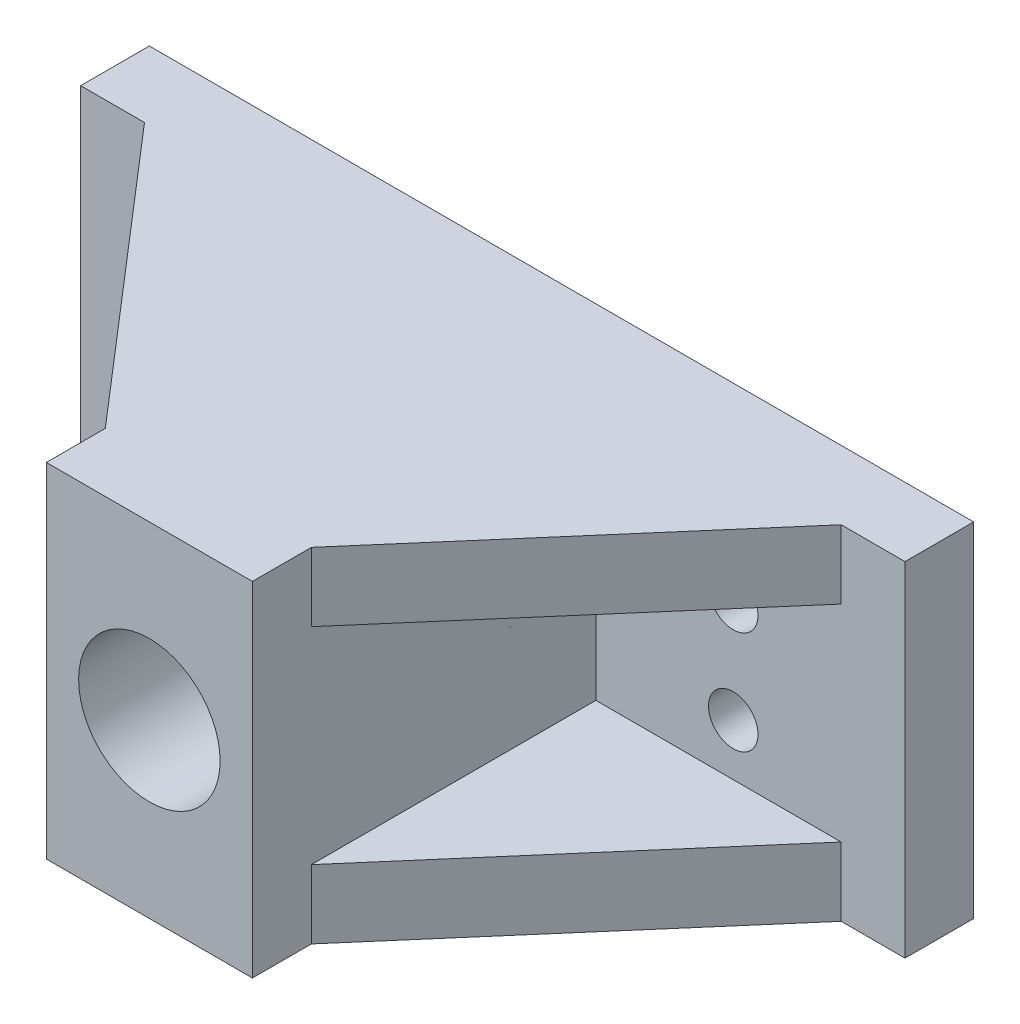
SolidWorks part; units mm, degrees
ref_plane "前视基准面" through (0, 0, 0) normal (0, 0, 1) x (1, 0, 0)
ref_plane "上视基准面" through (0, 0, 0) normal (0, 1, 0) x (1, 0, 0)
ref_plane "右视基准面" through (0, 0, 0) normal (1, 0, 0) x (0, 0, -1)
sketch "草图1" plane through (0, 0, 0) normal (0, 0, 1) x (1, 0, 0)
  line L1 (20, -7.5) -> (-20, -7.5)
  line L2 (20, -7.5) -> (20, 7.5)
  line L3 (20, 7.5) -> (-20, 7.5)
  line L4 (-20, -7.5) -> (-20, 7.5)
  line L5 (0, 7.5) -> (0, -7.5) construction
  line L6 (20, 0) -> (-20, 0) construction
  point P0 (0, 0)
  dimension "D1" = 15
  dimension "D2" = 40
extrude "凸台-拉伸1" add sketch "草图1" along normal blind 5
sketch "草图2" plane through (0, 0, 5) normal (0, 0, 1) x (1, 0, 0)
  line L0 (0, 0) -> (0, 16.7809) construction
  circle A0 centre (0, 0) radius 5.15
  circle A1 centre (-12, 0) radius 1.8
  circle A2 centre (12, 0) radius 1.8
  dimension "D1" = 10.3
  dimension "D2" = 3.6
  dimension "D3" = 12
extrude "切除-拉伸1" cut sketch "草图2" against normal blind 5
sketch "草图3" plane through (0, 0, 5) normal (0, 0, 1) x (1, 0, 0)
  line L0 (-7.5, 7.5) -> (-7.5, -7.5)
  line L1 (20, 7.5) -> (-20, 7.5) construction
  line L2 (-20, -7.5) -> (20, -7.5) construction
  line L3 (0, 7.5) -> (0, -7.5) construction
  line L4 (7.5, 7.5) -> (7.5, -7.5)
  line L5 (-7.5, 7.5) -> (7.5, 7.5)
  line L6 (-7.5, -7.5) -> (7.5, -7.5)
  circle A0 centre (0, 0) radius 5.05
  dimension "D1" = 15
extrude "凸台-拉伸2" add sketch "草图3" along normal blind 25
sketch "草图4" plane through (0, 0, 5) normal (0, 0, -1) x (-1, 0, 0)
  circle A0 centre (0, 0) radius 5.5
extrude "切除-拉伸2" cut sketch "草图4" against normal blind 31
sketch "草图5" plane through (0, 0, 5) normal (0, 0, 1) x (1, 0, 0)
  line L0 (-20, 7.5) -> (-30, 7.5)
  line L1 (-30, 7.5) -> (-30, -7.5)
  line L2 (-30, -7.5) -> (-20, -7.5)
  line L3 (-20, -7.5) -> (-20, 7.5)
  line L4 (0, 7.5) -> (0, -7.5) construction
  line L5 (7.5, 7.5) -> (-7.5, 7.5) construction
  line L6 (-7.5, -7.5) -> (7.5, -7.5) construction
  line L7 (30, -7.5) -> (20, -7.5)
  line L8 (20, -7.5) -> (20, 7.5)
  line L9 (20, 7.5) -> (30, 7.5)
  line L10 (30, 7.5) -> (30, -7.5)
  dimension "D1" = 10
extrude "凸台-拉伸3" add sketch "草图5" against normal blind 5
sketch "草图6" plane through (0, 0, 5) normal (0, 0, 1) x (1, 0, 0)
  line L0 (0, 0) -> (0, 14.0477) construction
  circle A0 centre (-24, 0) radius 1.8
  circle A1 centre (24, 0) radius 1.8
  circle A2 centre (-12, 0) radius 1.8 construction
  dimension "D1" = 3.6
  dimension "D2" = 12
extrude "切除-拉伸3" cut sketch "草图6" against normal blind 5
sketch "草图7" plane through (0, 0, 5) normal (0, 0, 1) x (1, 0, 0)
  line L0 (-30, 7.5) -> (-30, 12.5)
  line L1 (-30, 12.5) -> (30, 12.5)
  line L2 (30, 12.5) -> (30, 7.5)
  line L3 (30, 7.5) -> (-30, 7.5)
  line L4 (0, 0) -> (-30, 0) construction
  line L5 (-30, 7.5) -> (-30, -7.5) construction
  line L6 (-30, -12.5) -> (30, -12.5)
  line L7 (30, -12.5) -> (30, -7.5)
  line L8 (30, -7.5) -> (-30, -7.5)
  line L9 (-30, -7.5) -> (-30, -12.5)
  dimension "D1" = 5
extrude "凸台-拉伸4" add sketch "草图7" against normal blind 5
sketch "草图8" plane through (0, 0, 5) normal (0, 0, 1) x (1, 0, 0)
  line L0 (-7.5, 7.5) -> (-7.5, 12.5)
  line L1 (30, 12.5) -> (-30, 12.5) construction
  line L2 (-7.5, 12.5) -> (7.5, 12.5)
  line L3 (7.5, 12.5) -> (7.5, 7.5)
  line L4 (7.5, 7.5) -> (-7.5, 7.5)
  line L5 (-7.5, -7.5) -> (-7.5, -12.5)
  line L6 (-30, -12.5) -> (30, -12.5) construction
  line L7 (-7.5, -12.5) -> (7.5, -12.5)
  line L8 (7.5, -12.5) -> (7.5, -7.5)
  line L9 (7.5, -7.5) -> (-7.5, -7.5)
extrude "凸台-拉伸5" add sketch "草图8" along normal up to surface (25 mm away) up to face at (-5.5, 0, 30)
sketch "草图9" plane through (0, 12.5, 0) normal (0, 1, 0) x (1, 0, 0)
  line L0 (-25.3552, -5) -> (-7.5, -25.7076)
  line L1 (-7.5, -5) -> (-30, -5) construction
  line L2 (-7.5, -30) -> (-7.5, -5) construction
rib "筋1" sketch "草图9" sketch "草图9" thickness 5 extrusion direction parallel to sketch draft on no parameters "D1"=5
ref_plane "基准面1" through (0, 0, 0) normal (0, 1, 0) x (1, 0, 0)
mirror "镜向1" about plane through (0, 0, 0) normal (0, 1, 0) of "筋1"
ref_plane "基准面3" through (0, 0, 0) normal (-1, 0, 0) x (0, 0, 1)
mirror "镜向2" about plane through (0, 0, 0) normal (-1, 0, 0) of "镜向1", "筋1"
sketch "草图11" plane through (0, 0, 5) normal (0, 0, 1) x (1, 0, 0)
  circle A0 centre (-24, 0) radius 1.8
  circle A1 centre (-12, 0) radius 1.8
  circle A2 centre (12, 0) radius 1.8
  circle A3 centre (24, 0) radius 1.8
extrude "凸台-拉伸6" add sketch "草图11" against normal blind 5
sketch "草图12" plane through (0, 0, 5) normal (0, 0, 1) x (1, 0, 0)
  line L0 (0, 0) -> (-41.3935, 0) construction
  line L1 (-7.5, 7.5) -> (-7.5, 0) construction
  line L2 (-7.5, 12.5) -> (-7.5, -12.5) construction
  line L3 (0, 0) -> (0, 26.5844) construction
  circle A0 centre (-17.5, 3.75) radius 1.8
  circle A1 centre (-17.5, -3.75) radius 1.8
  circle A2 centre (17.5, -3.75) radius 1.8
  circle A3 centre (17.5, 3.75) radius 1.8
  point P10 (-7.5, 3.75)
  dimension "D1" = 3.6
  dimension "D2" = 10
extrude "切除-拉伸4" cut sketch "草图12" against normal blind 5
sketch "草图13" plane through (0, 0, 5) normal (0, 0, 1) x (1, 0, 0)
  circle A0 centre (0, 0) radius 5.15
  circle A1 centre (0, 0) radius 5.5
extrude "凸台-拉伸7" add sketch "草图13" along normal up to surface (25 mm away) up to face at (0, 0, 30)
